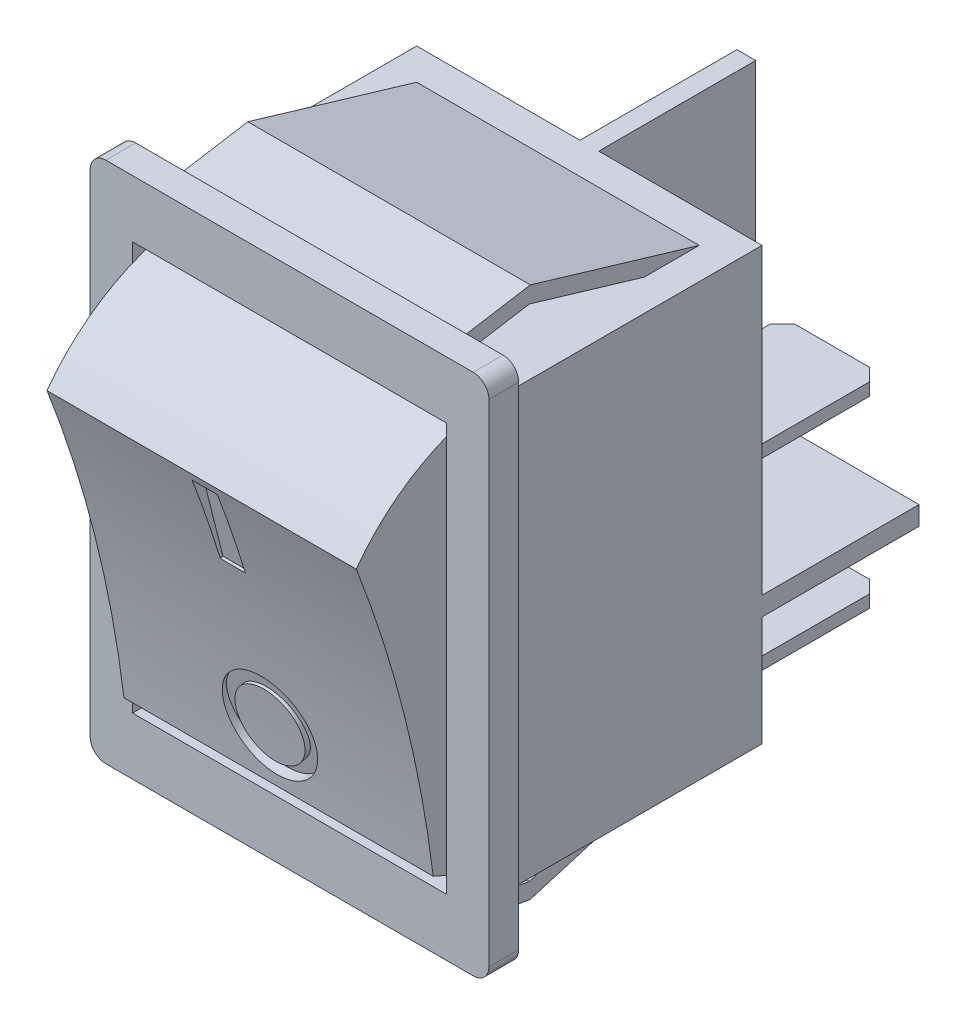
SolidWorks part; units mm, degrees
material "ABS PC"
ref_plane "Front" through (0, 0, 0) normal (0, 0, 1) x (1, 0, 0)
ref_plane "Top" through (0, 0, 0) normal (0, 1, 0) x (1, 0, 0)
ref_plane "Right" through (0, 0, 0) normal (1, 0, 0) x (0, 0, -1)
sketch "Sketch1" plane through (0, 0, 0) normal (0, 0, 1) x (1, 0, 0)
  line L1 (-11.7, -16.65) -> (11.7, -16.65)
  line L2 (-12.7, -15.65) -> (-12.7, 15.65)
  line L3 (-11.7, 16.65) -> (11.7, 16.65)
  line L4 (12.7, -15.65) -> (12.7, 15.65)
  line L5 (-10, -13) -> (10, -13)
  line L6 (-10, -13) -> (-10, 13)
  line L7 (-10, 13) -> (10, 13)
  line L8 (10, -13) -> (10, 13)
  arc A0 (-11.7, 16.65) -> (-12.7, 15.65) centre (-11.7, 15.65) ccw
  arc A1 (12.7, 15.65) -> (11.7, 16.65) centre (11.7, 15.65) ccw
  arc A2 (11.7, -16.65) -> (12.7, -15.65) centre (11.7, -15.65) ccw
  arc A3 (-12.7, -15.65) -> (-11.7, -16.65) centre (-11.7, -15.65) ccw
  point P12 (12.7, 16.65)
  point P15 (12.7, -16.65)
  point P18 (-12.7, -16.65)
  dimension "D9" = 1
  dimension "D1" = 25.4
  dimension "D2" = 12.7
  dimension "D3" = 33.3
  dimension "D4" = 16.65
  dimension "D5" = 20
  dimension "D6" = 10
  dimension "D7" = 26
  dimension "D8" = 13
extrude "Extrude1" add sketch "Sketch1" along normal blind 1.9
sketch "Sketch2" plane through (0, 0, 0) normal (0, 0, -1) x (-1, 0, 0)
  line L1 (-11, -13.75) -> (11, -13.75)
  line L2 (-11, -13.75) -> (-11, 13.75)
  line L3 (-11, 13.75) -> (11, 13.75)
  line L4 (11, -13.75) -> (11, 13.75)
  dimension "D1" = 22
  dimension "D2" = 11
  dimension "D3" = 27.5
  dimension "D4" = 13.75
extrude "Extrude2" add sketch "Sketch2" along normal blind 17.2
sketch "Sketch3" plane through (0, 0, 0) normal (0, 0, 1) x (1, 0, 0)
  line L1 (-9.85, -12.5) -> (9.85, -12.5)
  line L2 (-9.85, -12.5) -> (-9.85, 12.5)
  line L3 (-9.85, 12.5) -> (9.85, 12.5)
  line L4 (9.85, -12.5) -> (9.85, 12.5)
  dimension "D1" = 19.7
  dimension "D2" = 9.85
  dimension "D3" = 25
  dimension "D4" = 12.5
extrude "Extrude3" add sketch "Sketch3" along normal blind 7.6
sketch "Sketch4" plane through (-9.85, 0, 0) normal (-1, 0, 0) x (0, 0, 1)
  line L1 (0, -12.6491) -> (10.2, -12.6491)
  line L2 (0, 12.6491) -> (10.2, 12.6491)
  line L3 (10.2, 12.6491) -> (10.2, -12.6491)
  line L4 (2.596, -11.7339) -> (7.5, 7.6649)
  arc A0 (0, -12.6491) -> (2.596, -11.7339) centre (-3, 0) ccw
  arc A1 (7.5, 7.6649) -> (0, 12.6491) centre (-3, 0) ccw
  dimension "D2" = 26
  dimension "D1" = 3
  dimension "D3" = 10.2
  dimension "D4" = 7.5
extrude "Cut-Extrude1" cut sketch "Sketch4" along direction (-1, 0, 0) on the side against the normal up to next (19.7 mm away)
sketch "Sketch5" plane through (0, -1.3217, 5.2282) normal (0, -0.2451, 0.9695) x (1, 0, 0)
  line L1 (-0.8, 8.7214) -> (0.8, 8.7214)
  line L2 (-0.8, 8.7214) -> (-0.8, 3.2214)
  line L3 (-0.8, 3.2214) -> (0.8, 3.2214)
  line L4 (0.8, 8.7214) -> (0.8, 3.2214)
  circle A0 centre (0, -7) radius 3
  circle A1 centre (0, -7) radius 2.2
  dimension "D4" = 6
  dimension "D5" = 7
  dimension "D6" = 4.4
  dimension "D1" = 0.8
  dimension "D2" = 1.6
  dimension "D3" = 5.5
extrude "Cut-Extrude2" cut sketch "Sketch5" against normal blind 0.7
sketch "Sketch6" plane through (-9.85, 0, 0) normal (-1, 0, 0) x (0, 0, 1)
  line L0 (5.048, -2.0345) -> (82.608, -21.6418) construction
  line L1 (7.5, 7.6649) -> (2.596, -11.7339) construction
  circle A0 centre (82.608, -21.6418) radius 80.6231
  dimension "D1" = 80
extrude "Cut-Extrude3" cut sketch "Sketch6" against normal through all
sketch "Sketch7" plane through (0, 0, -17.2) normal (0, 0, -1) x (-1, 0, 0)
  line L0 (-11, -13.75) -> (11, -13.75) construction
  line L1 (-0.6, -13.75) -> (0.6, -13.75)
  line L2 (-0.6, -13.75) -> (-0.6, -6.75)
  line L3 (-0.6, 13.75) -> (0.6, 13.75)
  line L4 (0.6, -13.75) -> (0.6, -6.75)
  line L5 (11, 13.75) -> (-11, 13.75) construction
  line L6 (-11, 13.75) -> (-11, -13.75) construction
  line L7 (-11, -6.75) -> (-0.6, -6.75)
  line L8 (-11, -6.75) -> (-11, -5.55)
  line L9 (-11, -5.55) -> (-0.6, -5.55)
  line L10 (11, -6.75) -> (11, -5.55)
  line L11 (11, -13.75) -> (11, 13.75) construction
  line L12 (0.6, -5.55) -> (11, -5.55)
  line L13 (0.6, -6.75) -> (11, -6.75)
  line L14 (0.6, -5.55) -> (0.6, 13.75)
  line L15 (-0.6, -5.55) -> (-0.6, 13.75)
  line L17 (-8.65, -0.35) -> (-2.3, -0.35)
  line L18 (-8.65, -0.35) -> (-8.65, 0.45)
  line L19 (-8.65, 0.45) -> (-2.3, 0.45)
  line L20 (-2.3, -0.35) -> (-2.3, 0.45)
  line L21 (2.3, -0.35) -> (8.65, -0.35)
  line L22 (2.3, -0.35) -> (2.3, 0.45)
  line L23 (2.3, 0.45) -> (8.65, 0.45)
  line L24 (8.65, -0.35) -> (8.65, 0.45)
  line L25 (-8.65, -12.05) -> (-2.3, -12.05)
  line L26 (-8.65, -12.05) -> (-8.65, -11.25)
  line L27 (-8.65, -11.25) -> (-2.3, -11.25)
  line L28 (-2.3, -12.05) -> (-2.3, -11.25)
  line L29 (2.3, -12.05) -> (8.65, -12.05)
  line L30 (2.3, -12.05) -> (2.3, -11.25)
  line L31 (2.3, -11.25) -> (8.65, -11.25)
  line L32 (8.65, -12.05) -> (8.65, -11.25)
  dimension "D1" = 0.6
  dimension "D2" = 1.2
  dimension "D3" = 1.2
  dimension "D4" = 7
  dimension "D5" = 6.35
  dimension "D6" = 6.35
  dimension "D7" = 6.35
  dimension "D8" = 6.35
  dimension "D9" = 1.7
  dimension "D10" = 1.7
  dimension "D11" = 0.8
  dimension "D12" = 0.8
  dimension "D13" = 13.3
  dimension "D14" = 13.3
  dimension "D15" = 0.8
  dimension "D16" = 0.8
  dimension "D17" = 1.7
  dimension "D18" = 1.7
  dimension "D19" = 1.7
  dimension "D20" = 1.7
extrude "Extrude4" add sketch "Sketch7" along normal blind 10
chamfer "Chamfer1" distance 0.8 angle 45 8 edges at (8.65, -11.65, -27.2) (2.3, -11.65, -27.2) (-2.3, -11.65, -27.2) (-8.65, -11.65, -27.2) (-8.65, 0.05, -27.2) (-2.3, 0.05, -27.2) (2.3, 0.05, -27.2) (8.65, 0.05, -27.2)
sketch "Sketch8" plane through (0, 0, 0) normal (1, 0, 0) x (0, 0, -1)
  line L0 (-7.782, 0) -> (30.5239, 0) construction
  line L2 (15.2, 13.75) -> (4.4426, 16.95)
  line L4 (15.2, -13.75) -> (4.4426, -16.95)
  line L5 (4.4426, 16.95) -> (0.2, 16.25)
  line L6 (4.4426, -16.95) -> (0.2, -16.25)
  line L7 (0, -15.65) -> (0, 15.65) construction
  line L8 (-1.9, 16.65) -> (0, 16.65) construction
  line L9 (4.3782, 15.9259) -> (0.3628, 15.2633)
  line L10 (14.9149, 12.7915) -> (4.3782, 15.9259)
  line L11 (0.2, 16.25) -> (0.3628, 15.2633)
  line L12 (0.2, -16.25) -> (0.3628, -15.2633)
  line L13 (14.9149, 12.7915) -> (15.2, 13.75)
  line L14 (14.9149, -12.7915) -> (15.2, -13.75)
  line L15 (4.3782, -15.9259) -> (0.3628, -15.2633)
  line L16 (14.9149, -12.7915) -> (4.3782, -15.9259)
  dimension "D1" = 0.2
  dimension "D2" = 0.4
  dimension "D3" = 0.3
  dimension "D4" = 4.3
  dimension "D5" = 2
  dimension "D7" = 1
extrude "Extrude5" add sketch "Sketch8" along normal blind 9 and the other way blind 9
